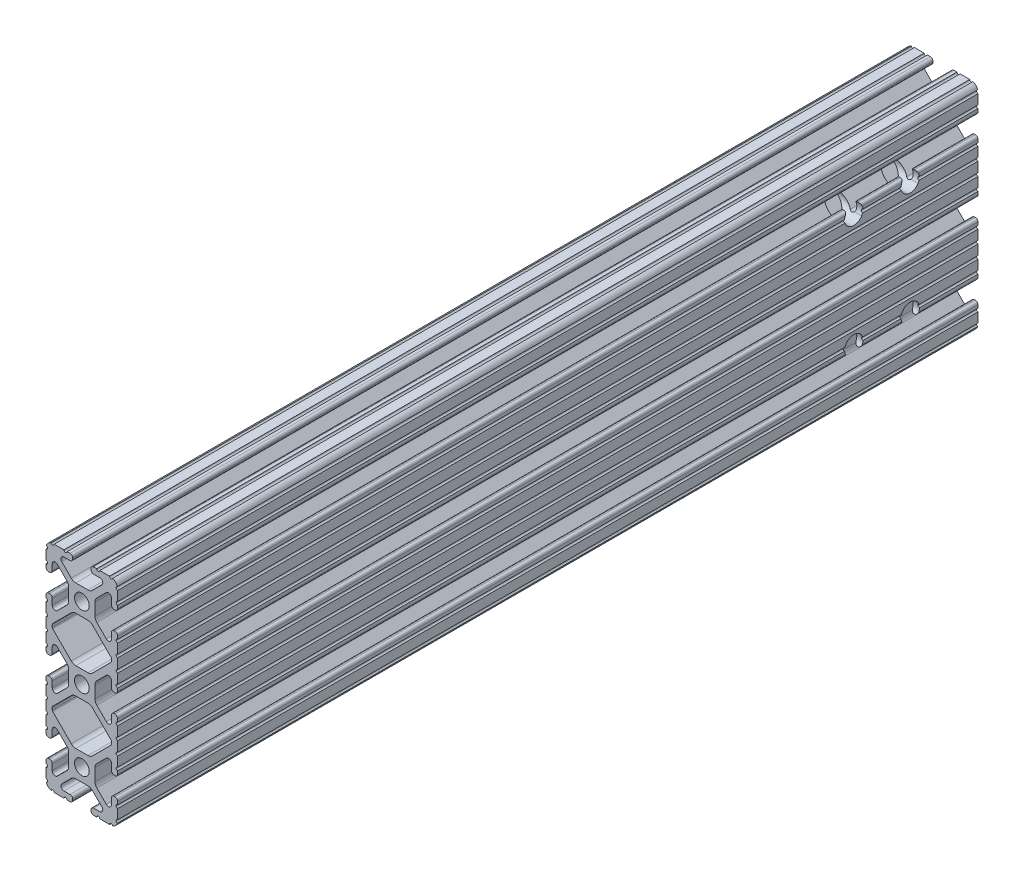
SolidWorks part; units mm, degrees
material "6061-T6 (SS)"
ref_plane "Front Plane" through (0, 0, 0) normal (0, 0, 1) x (1, 0, 0)
ref_plane "Top Plane" through (0, 0, 0) normal (0, 1, 0) x (1, 0, 0)
ref_plane "Right Plane" through (0, 0, 0) normal (1, 0, 0) x (0, 0, -1)
sketch "Sketch2" plane through (0, 0, 0) normal (0, 0, 1) x (1, 0, 0)
  line L0 (0, 38.1) -> (0, -38.1) construction
  line L1 (-12.7, 0) -> (12.7, 0) construction
  line L2 (3.2512, -38.1) -> (12.7, -38.1)
  line L3 (12.7, -38.1) -> (12.7, -28.6512)
  line L4 (3.2512, -38.1) -> (3.2512, -35.8902)
  line L5 (3.2512, -35.8902) -> (8.9276, -35.8902)
  line L6 (8.9276, -35.8902) -> (3.0856, -30.0482)
  line L7 (0, -25.4) -> (12.7, -38.1) construction
  line L8 (12.7, -28.6512) -> (10.4902, -28.6512)
  line L9 (10.4902, -28.6512) -> (10.4902, -34.3276)
  line L10 (10.4902, -34.3276) -> (4.6482, -28.4856)
  circle A0 centre (0, -25.4) radius 2.6035
  arc A1 (6.3485, -35.8902) -> (7.1039, -34.0665) centre (6.3485, -34.8219) ccw construction
  point P8 (0, -30.0482)
  dimension "Center Hole Diameter" = 5.207
  dimension "Rail Height" = 76.2
  dimension "Rail Width" = 25.4
  dimension "T-Slot Width" = 6.5024
  dimension "Slot Inner Width" = 14.8336
  dimension "Thickness" = 2.2098
  dimension "Slot Depth" = 5.842
  dimension "D1" = 2.2098
  dimension "D2" = 50.8
sketch "Sketch3" plane through (0, 0, 0) normal (1, 0, 0) x (0, 0, -1)
  line L0 (-152.4, -38.1) -> (152.4, -38.1) construction
  line L1 (-127, 0) -> (127, 0) construction
  dimension "D1" = 25.4
  dimension "Length" = 304.8
sketch "Sketch4" plane through (0, 0, 0) normal (0, 0, 1) x (1, 0, 0)
  line L0 (4.1904, -38.1) -> (10.1173, -38.1)
  line L1 (3.2512, -38.1) -> (12.7, -38.1) construction
  line L2 (3.2512, -38.1) -> (3.2512, -35.8902) construction
  line L3 (3.2512, -35.8902) -> (8.9276, -35.8902) construction
  line L4 (3.2512, -36.8294) -> (3.2512, -37.1608)
  line L5 (4.1904, -35.8902) -> (6.3485, -35.8902)
  line L6 (0, -30.0482) -> (2.164, -30.0482)
  line L7 (8.9276, -35.8902) -> (3.0856, -30.0482) construction
  line L8 (3.7373, -30.6999) -> (7.1039, -34.0665)
  line L9 (12.7, -38.1) -> (12.7, -28.6512) construction
  line L10 (10.4902, -34.3276) -> (4.6482, -28.4856) construction
  line L11 (10.4902, -28.6512) -> (10.4902, -34.3276) construction
  line L12 (10.4902, -31.7485) -> (10.4902, -29.5904)
  line L13 (12.7, -28.6512) -> (10.4902, -28.6512) construction
  line L14 (11.4294, -28.6512) -> (11.7608, -28.6512)
  line L15 (12.7, -29.5904) -> (12.7, -35.5173)
  line L16 (8.6665, -32.5039) -> (5.2999, -29.1373)
  line L17 (4.6482, -25.4) -> (4.6482, -27.564)
  line L19 (0, -30.0482) -> (0, -28.0035)
  line L20 (0, 38.1) -> (0, -38.1) construction
  line L21 (4.6482, -25.4) -> (2.6035, -25.4)
  arc A0 (3.2512, -37.1608) -> (4.1904, -38.1) centre (4.1904, -37.1608) ccw
  circle A1 centre (0, -25.4) radius 2.6035 construction
  arc A2 (3.2512, -36.8294) -> (4.1904, -35.8902) centre (4.1904, -36.8294) cw
  arc A3 (6.3485, -35.8902) -> (7.1039, -34.0665) centre (6.3485, -34.8219) ccw
  arc A4 (2.164, -30.0482) -> (3.7373, -30.6999) centre (2.164, -32.2732) cw
  arc A5 (10.1173, -38.1) -> (12.7, -35.5173) centre (10.1173, -35.5173) ccw
  arc A6 (8.6665, -32.5039) -> (10.4902, -31.7485) centre (9.4219, -31.7485) ccw
  arc A7 (10.4902, -29.5904) -> (11.4294, -28.6512) centre (11.4294, -29.5904) cw
  arc A8 (11.7608, -28.6512) -> (12.7, -29.5904) centre (11.7608, -29.5904) cw
  arc A9 (5.2999, -29.1373) -> (4.6482, -27.564) centre (6.8732, -27.564) cw
  arc A11 (0, -28.0035) -> (2.6035, -25.4) centre (0, -25.4) ccw
  dimension "D1" = 2.5827
  dimension "D2" = 2.225
  dimension "D3" = 0.9392
extrude "Boss-Extrude1" add sketch "Sketch4" along normal mid plane 304.8
sketch "Sketch5" plane through (0, 0, 0) normal (0, 0, 1) x (1, 0, 0)
  line L0 (3.2512, -38.1) -> (12.7, -38.1) construction
  line L1 (4.1904, -35.8902) -> (6.3485, -35.8902) construction
  line L3 (0, -25.4) -> (12.7, -38.1) construction
  line L4 (6.3485, -35.8902) -> (6.3485, -38.1) construction
  line L5 (8.9276, -35.8902) -> (3.0856, -30.0482) construction
  circle A0 centre (10.3562, -38.1) radius 0.5524
  circle A1 centre (5.796, -38.1) radius 0.5524
  circle A2 centre (12.7, -35.7562) radius 0.5525
  circle A3 centre (12.7, -31.196) radius 0.5525
  point P10 (5.2694, -35.8902)
  point P12 (9.4219, -31.7485)
  dimension "D1" = 1.1049
extrude "Cut-Extrude1" cut sketch "Sketch5" against normal through all both and the other way through all
mirror "Mirror1" about plane through (4.6482, -25.4, 152.4) normal (0, -1, 0) of bodies 137 134
sketch "Sketch6" plane through (0, 0, 0) normal (0, 0, 1) x (1, 0, 0)
  line L0 (12.7, -14.4914) -> (12.7, -12.7)
  line L1 (12.7, -12.7) -> (9.8037, -12.7)
  line L3 (9.8037, -12.7) -> (9.8037, -15.5963)
  line L4 (9.8037, -15.5963) -> (12.7, -15.5963)
  line L5 (6.3485, -12.7) -> (9.8037, -12.7) construction
  circle A0 centre (12.7, -15.0438) radius 0.5525 construction
  arc A1 (12.7, -14.4914) -> (12.7, -15.5963) centre (12.7, -15.0438) ccw
  arc A4 (9.8037, -12.7) -> (10.8954, -12.82) centre (10.3562, -12.7) ccw construction
extrude "Boss-Extrude2" add sketch "Sketch6" along normal mid plane 304.8
sketch "Sketch7" plane through (0, 0, 0) normal (0, 0, 1) x (1, 0, 0)
  line L0 (5.4206, -18.4168) -> (10.3284, -13.509)
  line L1 (3.7373, -20.1001) -> (7.1039, -16.7335) construction
  line L2 (10.4902, -13.1184) -> (10.4902, -12.7)
  line L3 (0, -12.7) -> (10.4902, -12.7)
  line L5 (0, -12.7) -> (5.4206, -18.4168)
  line L7 (0, 38.1) -> (0, -38.1) construction
  line L8 (6.3485, -12.7) -> (12.7, -12.7) construction
  arc A0 (10.3284, -13.509) -> (10.4902, -13.1184) centre (9.9377, -13.1184) ccw
  arc A3 (12.7, -14.4914) -> (12.7, -15.5963) centre (12.7, -15.0438) ccw construction
extrude "Cut-Extrude2" cut sketch "Sketch7" against normal through all both and the other way through all
mirror "Mirror2" about plane through (4.1904, -12.7, 152.4) normal (0, -1, 0) of bodies 139 135
other "SurfaceCut1"
mirror "Mirror3" about plane through (0, 0, 0) normal (1, 0, 0) of bodies 142 136
mirror "Mirror4" about plane through (0, 0, 0) normal (0, 1, 0) of bodies 140
sketch "Sketch8" plane through (-12.7, 0, 0) normal (-1, 0, 0) x (0, 0, 1)
  line L0 (-152.4, 0) -> (-118.4, 0) construction
  line L1 (-152.4, 2.164) -> (-152.4, -2.164) construction
  line L3 (-108.4, 20) -> (-128.4, 20) construction
  line L4 (-108.4, 20) -> (-108.4, -20) construction
  line L5 (-108.4, -20) -> (-128.4, -20) construction
  line L6 (-128.4, 20) -> (-128.4, -20) construction
  line L7 (-108.4, 20) -> (-128.4, -20) construction
  line L8 (-108.4, -20) -> (-128.4, 20) construction
  circle A0 centre (-108.4, 20) radius 3.2639
  circle A1 centre (-128.4, 20) radius 3.2639
  circle A2 centre (-128.4, -20) radius 3.2639
  circle A3 centre (-108.4, -20) radius 3.2639
  dimension "D4" = 6.5278
  dimension "D1" = 24
  dimension "D2" = 40
  dimension "D3" = 20
extrude "Cut-Extrude3" cut sketch "Sketch8" against normal through all
equation "\"D1@Sketch2\"= \"Thickness@Sketch2\""
equation "\"D2@Sketch4\"=\"Slot Inner Width@Sketch2\"*0.15"
equation "\"D1@Sketch4\"=\"D3@Sketch4\"*2.75"
equation "\"D3@Sketch4\"=\"Thickness@Sketch2\"*0.425"
equation "\"D1@Sketch5\"= \"Thickness@Sketch2\" * 0.5"
equation "\"azimuth_horizontal_rail_length\"=(\"altitude_horizontal_rail_length\"+6in-0.29in)"
equation "\"azimuth_vertictal_rail_length\"=6in"
equation "\"wall_screw_clearance_diameter\"=4.3mm"
equation "\"altitude_horizontal_rail_length\"=10in"
equation "\"altitude_vertictal_rail_length\"=12in"
equation "\"azimuth_vertictal_rail_length_short\"=(\"altitude_vertictal_rail_length\"-5in)"
equation "\"azimuth_vertictal_rail_length_long\"=(\"azimuth_vertictal_rail_length_short\"+4in)"
equation "\"table_length\"=72in"
equation "\"table_width\"=25in"
equation "\"table_thickness\"=1.75in"
equation "\"azimuth_mounting_hole_distance\"=9in"
equation "\"table_frame_vertical_length\"=12.5in"
equation "\"table_frame_diagonal_length\"=17.5in"
equation "\"linear_horizontal_rail_length\"=12in"
equation "\"D1@Boss-Extrude1\"=\"linear_horizontal_rail_length\""
equation "\"D1@Boss-Extrude2\"=\"linear_horizontal_rail_length\""
